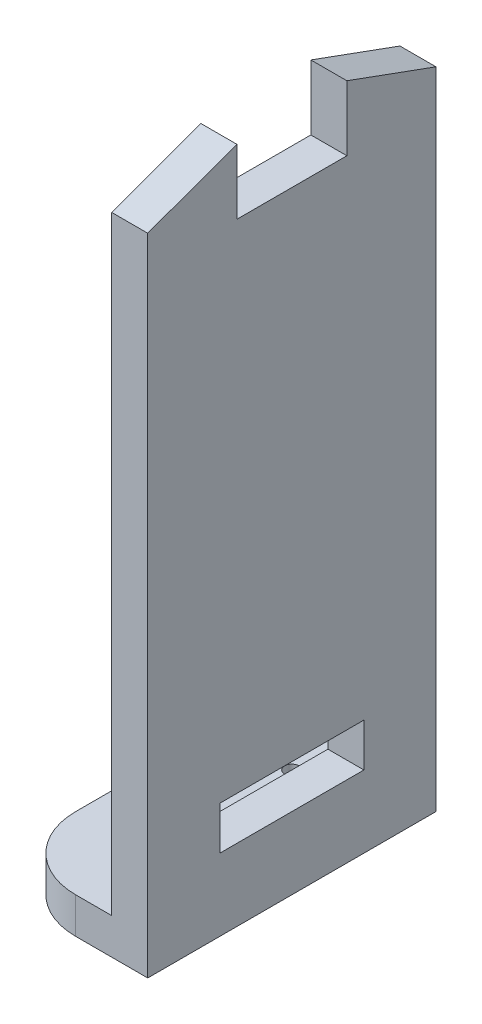
SolidWorks part; units mm, degrees
ref_plane "Front Plane" through (0, 0, 0) normal (0, 0, 1) x (1, 0, 0)
ref_plane "Top Plane" through (0, 0, 0) normal (0, 1, 0) x (1, 0, 0)
ref_plane "Right Plane" through (0, 0, 0) normal (1, 0, 0) x (0, 0, -1)
sketch "Sketch1" plane through (0, 0, 0) normal (0, 1, 0) x (1, 0, 0)
  line L0 (-6.0636, -8.0207) -> (3.9364, -8.0207)
  line L1 (3.9364, -8.0207) -> (3.9364, 31.9793)
  line L2 (3.9364, 31.9793) -> (-6.0636, 31.9793)
  line L3 (-16.0636, 21.9793) -> (-16.0636, 1.9793)
  circle A0 centre (-6.0636, 21.9793) radius 1
  circle A1 centre (-6.0636, 1.9793) radius 1
  arc A2 (-6.0636, 31.9793) -> (-16.0636, 21.9793) centre (-6.0636, 21.9793) ccw
  arc A3 (-16.0636, 1.9793) -> (-6.0636, -8.0207) centre (-6.0636, 1.9793) ccw
extrude "Boss-Extrude1" add sketch "Sketch1" along normal blind 5
sketch "Sketch5" plane through (3.9364, 0, 0) normal (1, 0, 0) x (0, 0, -1)
  line L0 (-8.0207, 5) -> (31.9793, 5)
  line L1 (31.9793, 5) -> (31.9793, 89.5078)
  line L2 (31.9793, 89.5078) -> (19.6127, 94.0156)
  line L3 (19.6127, 94.0156) -> (19.6127, 85)
  line L4 (19.6127, 85) -> (4.3458, 85)
  line L5 (4.3458, 85) -> (4.3458, 94.0156)
  line L6 (4.3458, 94.0156) -> (-8.0207, 89.5078)
  line L7 (-8.0207, 89.5078) -> (-8.0207, 5)
  point P0 (31.9793, 5)
extrude "Boss-Extrude2" add sketch "Sketch5" against normal blind 5
sketch "Sketch6" plane through (-1.0636, 0, 0) normal (-1, 0, 0) x (0, 0, 1)
  line L0 (-21.9793, 10) -> (-1.9793, 10)
  line L1 (-21.9793, 16) -> (-21.9793, 10)
  line L2 (-1.9793, 16) -> (-1.9793, 10)
  line L3 (-21.9793, 16) -> (-1.9793, 16)
  line L4 (-31.9793, 5) -> (8.0207, 5)
  line L9 (-19.6127, 85) -> (-19.6127, 94.0156)
  line L10 (-19.6127, 94.0156) -> (-31.9793, 89.5078)
  point P12 (-19.6127, 85)
extrude "Cut-Extrude1" cut sketch "Sketch6" against normal blind 5 contours L3 L1 L0 L2
sketch "Sketch7" plane through (-1.0636, 0, 0) normal (-1, 0, 0) x (0, 0, 1)
  line L0 (-11.9793, 85) -> (-11.9793, 60.54) construction
  line L1 (-19.6127, 85) -> (-4.3458, 85) construction
  circle A0 centre (-11.9793, 60.54) radius 1
  dimension "D2" = 2
  dimension "D1" = 24.46
